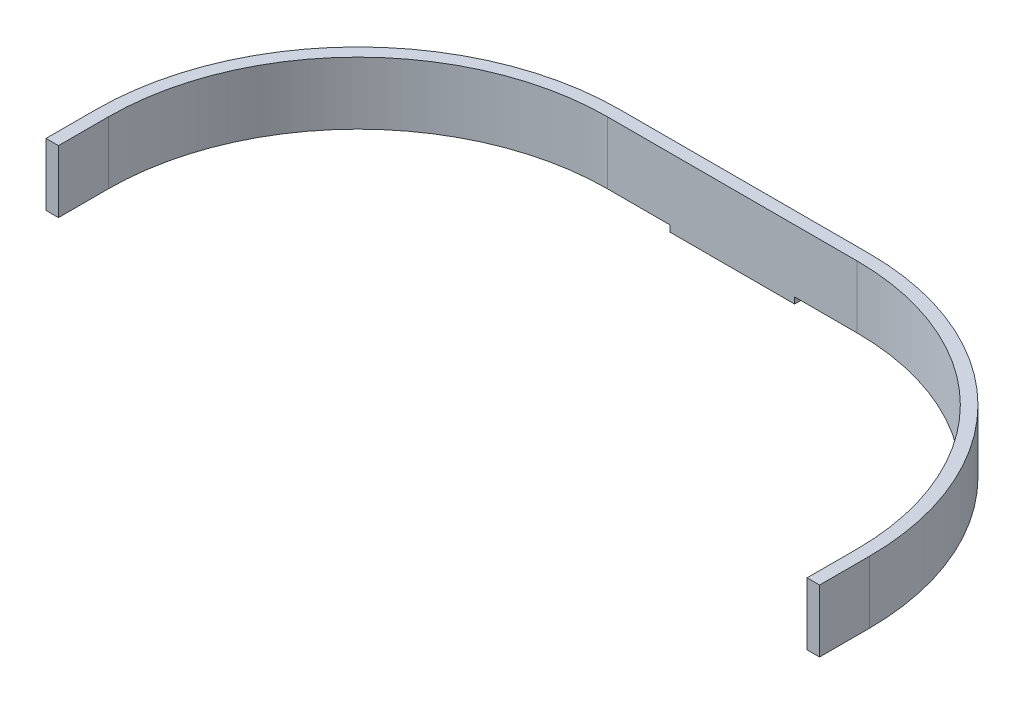
SolidWorks part; units mm, degrees
ref_plane "Front" through (0, 0, 0) normal (0, 0, 1) x (1, 0, 0)
ref_plane "Top" through (0, 0, 0) normal (0, 1, 0) x (1, 0, 0)
ref_plane "Right" through (0, 0, 0) normal (1, 0, 0) x (0, 0, -1)
sketch "草图2" plane through (0, 0, 0) normal (1, 0, 0) x (0, 0, -1)
  line L0 (0, 0) -> (-13.2631, 0) construction
  line L1 (-10, 1) -> (-8, 1)
  line L3 (-10, -1) -> (-8, -1)
  line L5 (0, 0) -> (0, 8.7818) construction
  line L6 (-18.7262, 30) -> (26.9936, 30) construction
  line L7 (-8, 1) -> (-8, -1)
  line L21 (-10, -1) -> (-12, -1)
  line L22 (-10, 1) -> (-12, 1)
  line L25 (-12, 1) -> (-12, -1)
  dimension "D1" = 1
  dimension "D2" = 2
  dimension "D3" = 2
  dimension "D5" = 30
extrude "凸台-拉伸1" add sketch "草图2" along normal mid plane 40
sketch "草图9" plane through (0, 1, 0) normal (0, 1, 0) x (1, 0, 0)
  line L0 (0, 10) -> (0, 6) construction
  line L2 (-20, -12) -> (46.4824, -12) construction
  line L3 (0, -12) -> (0, -115.9508) construction
  line L6 (-105.6347, -92) -> (112.3187, -92) construction
  line L11 (-40, -92) -> (40, -92) construction
  line L20 (-40, -8) -> (40, -8)
  line L22 (-40, -92) -> (40, -92) construction
  line L23 (-40, -12) -> (40, -12)
  line L29 (-124, -92) -> (-124, -108)
  line L30 (-124, -108) -> (-120, -108)
  line L31 (-120, -92) -> (-120, -108)
  line L33 (120, -92) -> (120, -108)
  line L34 (120, -108) -> (124, -108)
  line L35 (124, -92) -> (124, -108)
  arc A4 (-40, -8) -> (-124, -92) centre (-40, -92) ccw
  arc A5 (124, -92) -> (40, -8) centre (40, -92) ccw
  arc A6 (-40, -12) -> (-120, -92) centre (-40, -92) ccw
  arc A7 (120, -92) -> (40, -12) centre (40, -92) ccw
  point P7 (0, -92)
  point P10 (0, -92)
  point P13 (0, -92)
  point P19 (0, -92)
  dimension "D2" = 16
  dimension "D1" = 80
  dimension "D3" = 16
extrude "凸台-拉伸4" add sketch "草图9" along normal blind 20
sketch "草图10" plane through (0, 0, 8) normal (0, 0, -1) x (-1, 0, 0)
  line L0 (0, 0) -> (0, 32.271) construction
  line L1 (-40, 11) -> (40, 11) construction
  line L2 (-40, 21) -> (-40, 1) construction
  line L3 (40, 21) -> (40, 1) construction
  circle A0 centre (0, 11) radius 6
extrude "凸台-拉伸5" add sketch "草图10" along normal blind 4
